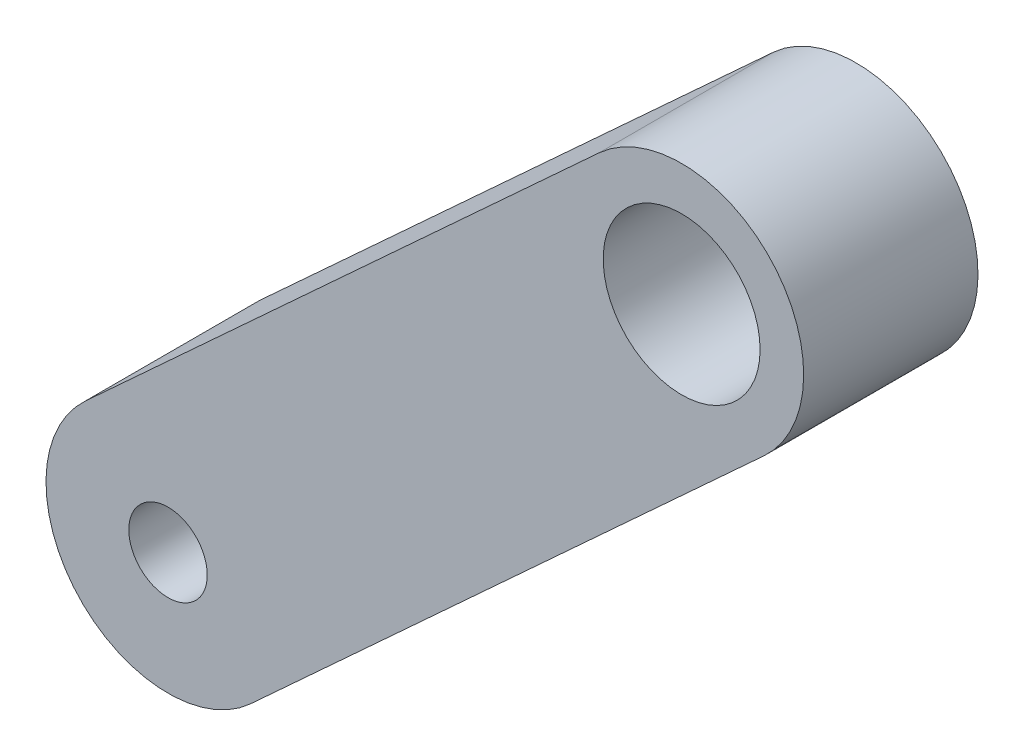
SolidWorks part; units mm, degrees
ref_plane "Front Plane" through (0, 0, 0) normal (0, 0, 1) x (1, 0, 0)
ref_plane "Top Plane" through (0, 0, 0) normal (0, 1, 0) x (1, 0, 0)
ref_plane "Right Plane" through (0, 0, 0) normal (1, 0, 0) x (0, 0, -1)
sketch "Sketch1" plane through (0, 0, 0) normal (0, 0, 1) x (1, 0, 0)
  line L0 (0, 0) -> (294.6187, 270.5547) construction
  line L1 (-47.3471, 51.5583) -> (247.2716, 322.1129)
  line L2 (47.3471, -51.5583) -> (341.9658, 218.9964)
  arc A0 (-47.3471, 51.5583) -> (47.3471, -51.5583) centre (0, 0) ccw
  arc A1 (341.9658, 218.9964) -> (247.2716, 322.1129) centre (294.6187, 270.5547) ccw
  circle A2 centre (0, 0) radius 22.5
  circle A3 centre (294.6187, 270.5547) radius 45
  point P3 (147.3093, 135.2773)
  dimension "D1" = 45
  dimension "D2" = 90
  dimension "D4" = 70
  dimension "D3" = 400
extrude "Boss-Extrude1" add sketch "Sketch1" along normal blind 100
